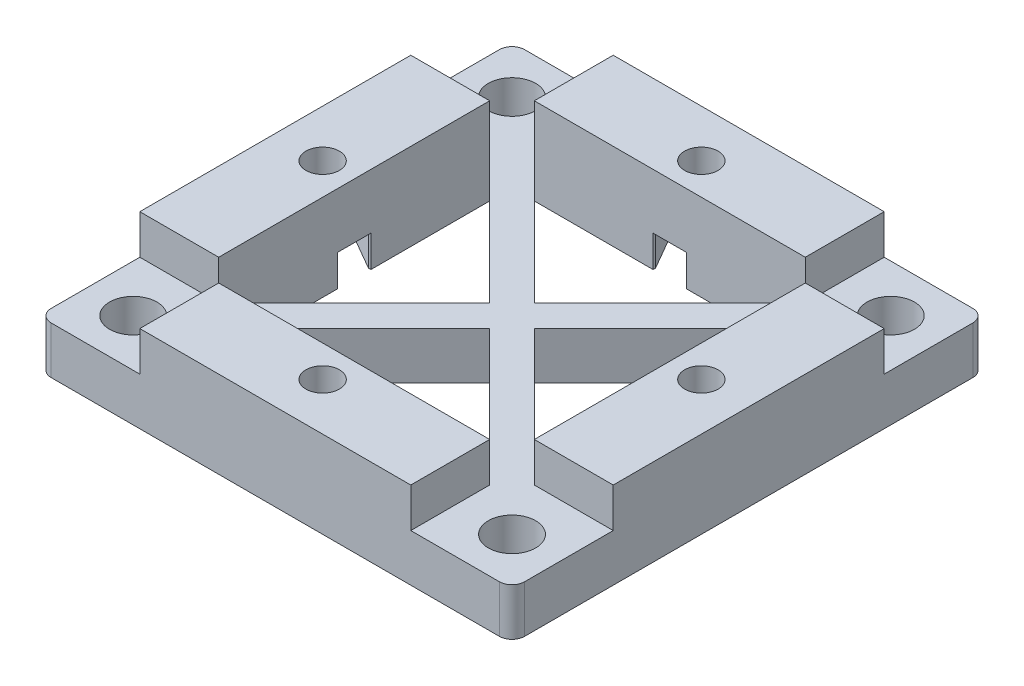
SolidWorks part; units mm, degrees
ref_plane "Front Plane" through (0, 0, 0) normal (0, 0, 1) x (1, 0, 0)
ref_plane "Top Plane" through (0, 0, 0) normal (0, 1, 0) x (1, 0, 0)
ref_plane "Right Plane" through (0, 0, 0) normal (1, 0, 0) x (0, 0, -1)
sketch "Sketch1" plane through (0, 0, 0) normal (0, 1, 0) x (1, 0, 0)
  line L0 (9.525, 0) -> (9.525, -95.25) construction
  line L1 (0, 0) -> (95.25, 0)
  line L2 (0, 0) -> (0, -95.25)
  line L3 (0, -95.25) -> (95.25, -95.25)
  line L4 (95.25, 0) -> (95.25, -95.25)
  line L5 (15.875, -15.875) -> (79.375, -15.875)
  line L6 (15.875, -15.875) -> (15.875, -79.375)
  line L7 (15.875, -79.375) -> (79.375, -79.375)
  line L8 (79.375, -15.875) -> (79.375, -79.375)
  line L9 (85.725, 0) -> (85.725, -95.25) construction
  line L10 (0, -9.525) -> (95.25, -9.525) construction
  line L11 (0, -85.725) -> (95.25, -85.725) construction
  line L12 (15.875, -15.875) -> (79.375, -79.375)
  line L13 (15.875, -79.375) -> (79.375, -15.875)
  line L14 (18.1201, -81.6201) -> (81.6201, -18.1201)
  line L15 (13.6299, -18.1201) -> (77.1299, -81.6201)
  line L16 (13.6299, -77.1299) -> (77.1299, -13.6299)
  line L17 (18.1201, -13.6299) -> (81.6201, -77.1299)
  circle A0 centre (9.525, -9.525) radius 4.7625
  circle A1 centre (9.525, -85.725) radius 4.7625
  circle A2 centre (85.725, -85.725) radius 4.7625
  circle A4 centre (85.725, -9.525) radius 4.7625
  dimension "D9" = 9.525
  dimension "D10" = 9.525
  dimension "D11" = 9.525
  dimension "D12" = 3.175
  dimension "D13" = 9.525
  dimension "D1" = 15.875
  dimension "D2" = 15.875
  dimension "D3" = 15.875
  dimension "D4" = 15.875
  dimension "D5" = 9.525
  dimension "D6" = 9.525
  dimension "D7" = 9.525
  dimension "D8" = 9.525
  dimension "D14" = 76.2
  dimension "D15" = 76.2
  dimension "D16" = 3.175
extrude "Boss-Extrude1" add sketch "Sketch1" along normal blind 9.525
sketch "Sketch2" plane through (0, 9.525, 0) normal (0, 1, 0) x (1, 0, 0)
  line L4 (47.625, -52.1151) -> (74.8849, -79.375) construction
  line L5 (20.3651, -79.375) -> (47.625, -52.1151) construction
  line L6 (20.3651, -79.375) -> (74.8849, -79.375) construction
  line L7 (79.375, -20.3651) -> (79.375, -74.8849) construction
  line L20 (95.25, -95.25) -> (95.25, 0)
  line L21 (95.25, 0) -> (0, 0)
  line L22 (0, 0) -> (0, -95.25)
  line L23 (0, -95.25) -> (95.25, -95.25)
  line L24 (95.25, -95.25) -> (95.25, 0)
  line L25 (95.25, 0) -> (0, 0)
  line L26 (0, 0) -> (0, -95.25)
  line L27 (0, -95.25) -> (95.25, -95.25)
  line L28 (52.1151, -47.625) -> (79.375, -74.8849) construction
  line L29 (52.1151, -47.625) -> (79.375, -20.3651) construction
  line L30 (47.625, -43.1349) -> (74.8849, -15.875) construction
  line L31 (15.875, -74.8849) -> (43.1349, -47.625) construction
  line L32 (15.875, -20.3651) -> (15.875, -74.8849) construction
  line L33 (15.875, -20.3651) -> (43.1349, -47.625) construction
  line L34 (20.3651, -15.875) -> (74.8849, -15.875) construction
  line L35 (20.3651, -15.875) -> (47.625, -43.1349) construction
  line L36 (47.625, -52.1151) -> (74.8849, -79.375)
  line L37 (20.3651, -79.375) -> (47.625, -52.1151)
  line L38 (20.3651, -79.375) -> (74.8849, -79.375)
  line L39 (79.375, -20.3651) -> (79.375, -74.8849)
  line L40 (52.1151, -47.625) -> (79.375, -74.8849)
  line L41 (52.1151, -47.625) -> (79.375, -20.3651)
  line L42 (47.625, -43.1349) -> (74.8849, -15.875)
  line L43 (15.875, -74.8849) -> (43.1349, -47.625)
  line L44 (15.875, -20.3651) -> (15.875, -74.8849)
  line L45 (15.875, -20.3651) -> (43.1349, -47.625)
  line L46 (20.3651, -15.875) -> (74.8849, -15.875)
  line L47 (20.3651, -15.875) -> (47.625, -43.1349)
  dimension "D1" = 0
extrude "Boss-Extrude2" [suppressed] add sketch "Sketch2" along normal blind 3.175
fillet "Fillet1" radius 2.54 4 edges at (95.25, 4.7625, 0) (0, 4.7625, 0) (95.25, 4.7625, 95.25) (0, 4.7625, 95.25)
sketch "Sketch3" plane through (0, 9.525, 0) normal (0, 1, 0) x (1, 0, 0)
  line L0 (74.8849, -79.375) -> (74.8849, 0)
  line L1 (2.54, 0) -> (92.71, 0) construction
  line L2 (20.3651, -15.875) -> (20.3651, -95.25)
  line L3 (2.54, -95.25) -> (92.71, -95.25) construction
  line L4 (15.875, -74.8849) -> (95.25, -74.8849)
  line L5 (95.25, -2.54) -> (95.25, -92.71) construction
  line L6 (79.375, -20.3651) -> (0, -20.3651)
  line L7 (0, -2.54) -> (0, -92.71) construction
  line L9 (74.8849, -79.375) -> (20.3651, -79.375)
  line L10 (74.8849, -79.375) -> (74.8849, -95.25)
  line L11 (74.8849, -95.25) -> (20.3651, -95.25)
  line L12 (20.3651, -79.375) -> (20.3651, -95.25)
  line L13 (15.875, -74.8849) -> (0, -74.8849)
  line L14 (15.875, -74.8849) -> (15.875, -20.3651)
  line L15 (15.875, -20.3651) -> (0, -20.3651)
  line L16 (0, -74.8849) -> (0, -20.3651)
  line L17 (20.3651, -15.875) -> (74.8849, -15.875)
  line L18 (20.3651, -15.875) -> (20.3651, 0)
  line L19 (20.3651, 0) -> (74.8849, 0)
  line L20 (74.8849, -15.875) -> (74.8849, 0)
  line L21 (79.375, -20.3651) -> (95.25, -20.3651)
  line L22 (79.375, -20.3651) -> (79.375, -74.8849)
  line L23 (79.375, -74.8849) -> (95.25, -74.8849)
  line L24 (95.25, -20.3651) -> (95.25, -74.8849)
  line M3 (79.375, -20.3651) -> (79.375, -74.8849)
  line M6 (20.3651, -15.875) -> (74.8849, -15.875)
  line M9 (74.8849, -79.375) -> (20.3651, -79.375)
  line M12 (15.875, -74.8849) -> (15.875, -20.3651)
  line M17 (2.54, -95.25) -> (92.71, -95.25)
  line M19 (95.25, -92.71) -> (95.25, -2.54)
  line M21 (92.71, 0) -> (2.54, 0)
  line M23 (0, -2.54) -> (0, -92.71)
extrude "Boss-Extrude3" add sketch "Sketch3" along normal blind 7.9375 contours L10 L2 M9 M17 | L21 L4 M3 M19 | L18 L0 M6 M21 | L13 L6 M12 M23 | L17 L20
sketch "Sketch4" plane through (0, 17.4625, 0) normal (0, 1, 0) x (1, 0, 0)
  line L0 (95.25, -47.625) -> (0, -47.625)
  line L1 (95.25, -74.8849) -> (95.25, -20.3651) construction
  line L2 (0, -20.3651) -> (0, -74.8849) construction
  line L3 (47.625, -95.25) -> (47.625, 0)
  line L4 (20.3651, -95.25) -> (74.8849, -95.25) construction
  line L5 (74.8849, 0) -> (20.3651, 0) construction
  circle A0 centre (85.725, -47.625) radius 3.3734
  circle A1 centre (47.625, -85.725) radius 3.3734
  circle A2 centre (9.525, -47.625) radius 3.3734
  circle A3 centre (47.625, -9.525) radius 3.3734
  dimension "D1" = 6.7469
  dimension "D2" = 38.1
  dimension "D3" = 38.1
  dimension "D4" = 38.1
  dimension "D5" = 38.1
extrude "Cut-Extrude1" cut sketch "Sketch4" against normal through all
sketch "Sketch5" plane through (0, 0, 0) normal (0, -1, 0) x (1, 0, 0)
  line L1 (40.8792, 85.725) -> (44.2521, 79.883)
  line L2 (44.2521, 79.883) -> (50.9979, 79.883)
  line L3 (50.9979, 79.883) -> (54.3708, 85.725)
  line L4 (54.3708, 85.725) -> (50.9979, 91.567)
  line L5 (50.9979, 91.567) -> (44.2521, 91.567)
  line L6 (44.2521, 91.567) -> (40.8792, 85.725)
  line L7 (79.883, 44.2521) -> (85.725, 40.8792)
  line L8 (85.725, 40.8792) -> (91.567, 44.2521)
  line L9 (91.567, 44.2521) -> (91.567, 50.9979)
  line L10 (91.567, 50.9979) -> (85.725, 54.3708)
  line L11 (85.725, 54.3708) -> (79.883, 50.9979)
  line L12 (79.883, 50.9979) -> (79.883, 44.2521)
  line L13 (9.525, 54.3708) -> (3.683, 50.9979)
  line L14 (3.683, 50.9979) -> (3.683, 44.2521)
  line L15 (3.683, 44.2521) -> (9.525, 40.8792)
  line L16 (9.525, 40.8792) -> (15.367, 44.2521)
  line L17 (15.367, 44.2521) -> (15.367, 50.9979)
  line L18 (15.367, 50.9979) -> (9.525, 54.3708)
  line L19 (40.8792, 9.525) -> (44.2521, 3.683)
  line L20 (44.2521, 3.683) -> (50.9979, 3.683)
  line L21 (50.9979, 3.683) -> (54.3708, 9.525)
  line L22 (54.3708, 9.525) -> (50.9979, 15.367)
  line L23 (50.9979, 15.367) -> (44.2521, 15.367)
  line L24 (44.2521, 15.367) -> (40.8792, 9.525)
  line L26 (79.883, 44.2521) -> (79.375, 44.2521)
  line L27 (79.375, 20.3651) -> (79.375, 74.8849) construction
  line L28 (79.375, 44.2521) -> (79.375, 50.9979)
  line L29 (79.375, 50.9979) -> (79.883, 50.9979)
  line L30 (20.3651, 79.375) -> (74.8849, 79.375) construction
  line L31 (50.9979, 79.883) -> (44.2521, 79.883)
  line L32 (50.9979, 79.883) -> (50.9979, 79.375)
  line L33 (50.9979, 79.375) -> (44.2521, 79.375)
  line L34 (44.2521, 79.883) -> (44.2521, 79.375)
  line L35 (15.875, 20.3651) -> (15.875, 74.8849) construction
  line L36 (15.367, 44.2521) -> (15.875, 44.2521)
  line L37 (15.367, 44.2521) -> (15.367, 50.9979)
  line L38 (15.367, 50.9979) -> (15.875, 50.9979)
  line L39 (15.875, 44.2521) -> (15.875, 50.9979)
  line L40 (20.3651, 15.875) -> (74.8849, 15.875) construction
  line L41 (50.9979, 15.367) -> (44.2521, 15.367)
  line L42 (50.9979, 15.367) -> (50.9979, 15.875)
  line L43 (50.9979, 15.875) -> (44.2521, 15.875)
  line L44 (44.2521, 15.367) -> (44.2521, 15.875)
  circle A0 centre (47.625, 85.725) radius 5.842 construction
  circle A1 centre (85.725, 47.625) radius 5.842 construction
  circle A2 centre (9.525, 47.625) radius 5.842 construction
  circle A3 centre (47.625, 9.525) radius 5.842 construction
  circle M7 centre (85.725, 47.625) radius 3.3734
  circle M8 centre (47.625, 9.525) radius 3.3734
  circle M9 centre (9.525, 47.625) radius 3.3734
  circle M10 centre (47.625, 85.725) radius 3.3734
  line M12 (79.375, 74.8849) -> (79.375, 20.3651)
  line M15 (74.8849, 15.875) -> (20.3651, 15.875)
  line M18 (20.3651, 79.375) -> (74.8849, 79.375)
  line M21 (15.875, 20.3651) -> (15.875, 74.8849)
  dimension "D1" = 11.684
  dimension "D2" = 11.684
  dimension "D3" = 11.684
  dimension "D4" = 11.684
extrude "Cut-Extrude2" cut sketch "Sketch5" against normal blind 6.35 contours L11 L12 L7 L8 L9 L10 M7 | L29 L26 L12 M12 | L5 L6 L1 L2 L3 L4 M10 | L2 L34 L32 M18 | L17 L18 L13 L14 L15 L16 M9 | L38 L17 L36 M21 | L23 L24 L19 L20 L21 L22 M8 | L44 L23 L42 M15
ref_plane "Plane1" through (0, 0, 47.625) normal (0, 0, 1) x (1, 0, 0)
ref_plane "Plane2" through (0, 0, 0) normal (-0.7071, 0, 0.7071) x (0.7071, 0, 0.7071)
ref_plane "Plane3" through (0, 0, 0) normal (-0.7071, 0, 0.7071) x (0.7071, 0, 0.7071)
ref_plane "Plane4" through (47.625, 0, 0) normal (1, 0, 0) x (0, 0, -1)
